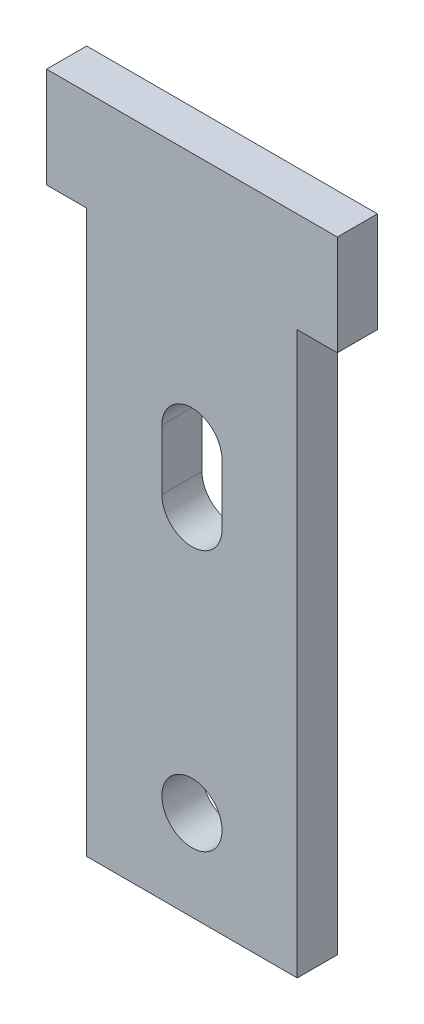
SolidWorks part; units mm, degrees
ref_plane "Front Plane" through (0, 0, 0) normal (0, 0, 1) x (1, 0, 0)
ref_plane "Top Plane" through (0, 0, 0) normal (0, 1, 0) x (1, 0, 0)
ref_plane "Right Plane" through (0, 0, 0) normal (1, 0, 0) x (0, 0, -1)
sketch "Sketch1" plane through (0, 0, 0) normal (0, 1, 0) x (1, 0, 0)
  line L1 (-6.6675, -1.27) -> (6.6675, -1.27)
  line L2 (-6.6675, -1.27) -> (-6.6675, 1.27)
  line L3 (-6.6675, 1.27) -> (6.6675, 1.27)
  line L4 (6.6675, -1.27) -> (6.6675, 1.27)
  line L5 (-6.6675, -1.27) -> (6.6675, 1.27) construction
  line L6 (-6.6675, 1.27) -> (6.6675, -1.27) construction
  point P0 (0, 0)
  dimension "D1" = 2.54
  dimension "D2" = 13.335
extrude "Boss-Extrude1" add sketch "Sketch1" along normal blind 35.56
sketch "Sketch2" plane through (0, 0, 1.27) normal (0, 0, 1) x (1, 0, 0)
  line L0 (-6.6675, 35.56) -> (6.6675, 35.56) construction
  line L1 (-6.6675, 35.56) -> (6.6675, 35.56)
  line L2 (0, 35.56) -> (0, 7.0568) construction
  line L3 (6.6675, 35.56) -> (9.2075, 35.56)
  line L4 (9.2075, 35.56) -> (9.2075, 41.91)
  line L5 (-9.2075, 35.56) -> (-9.2075, 41.91)
  line L6 (-6.6675, 35.56) -> (-9.2075, 35.56)
  line L7 (-9.2075, 41.91) -> (9.2075, 41.91)
  line M10 (6.6675, 35.56) -> (-6.6675, 35.56)
  dimension "D1" = 2.54
  dimension "D2" = 6.35
extrude "Boss-Extrude2" add sketch "Sketch2" against normal up to surface (2.54 mm away) contours L7 L5 L6 L1 L3 L4 M10 up to face at (0, 17.78, -1.27)
sketch "Sketch3" plane through (0, 0, 1.27) normal (0, 0, 1) x (1, 0, 0)
  line L0 (0, 0) -> (0, 3.81) construction
  line L1 (0, 7.62) -> (0, 20.32) construction
  line L2 (0, 26.035) -> (0, 22.225) construction
  line L3 (1.905, 26.035) -> (1.905, 22.225)
  line L4 (-1.905, 26.035) -> (-1.905, 22.225)
  circle A0 centre (0, 5.715) radius 1.905
  arc A1 (1.905, 26.035) -> (-1.905, 26.035) centre (0, 26.035) ccw
  arc A2 (-1.905, 22.225) -> (1.905, 22.225) centre (0, 22.225) ccw
  point P9 (0, 24.13)
  point P14 (0, 27.94)
  point P15 (0, 20.32)
  dimension "D2" = 3.81
  dimension "D1" = 3.81
  dimension "D3" = 12.7
  dimension "D4" = 7.62
extrude "Cut-Extrude1" cut sketch "Sketch3" against normal up to next
